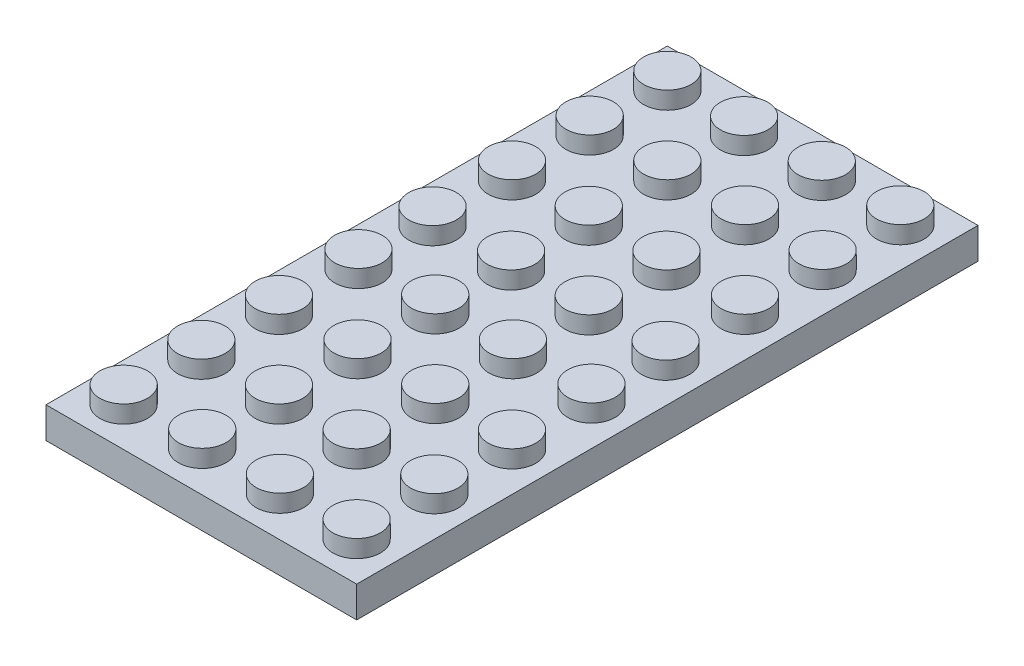
SolidWorks part; units mm, degrees
ref_plane "Front Plane" through (0, 0, 0) normal (0, 0, 1) x (1, 0, 0)
ref_plane "Top Plane" through (0, 0, 0) normal (0, 1, 0) x (1, 0, 0)
ref_plane "Right Plane" through (0, 0, 0) normal (1, 0, 0) x (0, 0, -1)
sketch "Sketch3" plane through (0, 0, 0) normal (0, 1, 0) x (1, 0, 0)
  line L0 (-16, 32) -> (-16, -32)
  line L4 (-16, 32) -> (16, 32)
  line L5 (16, 32) -> (16, -32)
  line L6 (16, -32) -> (-16, -32)
  dimension "D1" = 64
  dimension "D2" = 32
extrude "Boss-Extrude2" add sketch "Sketch3" along normal blind 3.2 contours L0 L6 L5 L4
sketch "Sketch4" plane through (0, 3.2, 0) normal (0, 1, 0) x (1, 0, 0)
  line L0 (-16, 32) -> (16, 32) construction
  circle A0 centre (-12, 28) radius 2.45
  circle A1 centre (-4, 27.9085) radius 2.45
  circle A2 centre (4, 27.9085) radius 2.45
  circle A3 centre (12, 28) radius 2.45
  circle A4 centre (12, 20) radius 2.45
  circle A5 centre (4, 20) radius 2.45
  circle A6 centre (-4, 20) radius 2.45
  circle A7 centre (-12, 20) radius 2.45
  circle A8 centre (12, 12) radius 2.45
  circle A9 centre (12, 3.817) radius 2.45
  circle A10 centre (4, 3.9085) radius 2.45
  circle A11 centre (4, 11.9085) radius 2.45
  circle A12 centre (-4, 11.9085) radius 2.45
  circle A13 centre (-4, 3.9085) radius 2.45
  circle A14 centre (-12, 3.817) radius 2.45
  circle A15 centre (-12, 12) radius 2.45
  circle A16 centre (4, -27.9085) radius 2.45
  circle A17 centre (12, -28) radius 2.45
  circle A18 centre (12, -20) radius 2.45
  circle A19 centre (4, -20) radius 2.45
  circle A20 centre (4, -11.9085) radius 2.45
  circle A21 centre (12, -12) radius 2.45
  circle A22 centre (12, -3.817) radius 2.45
  circle A23 centre (4, -3.9085) radius 2.45
  circle A24 centre (-4, -3.9085) radius 2.45
  circle A25 centre (-4, -11.9085) radius 2.45
  circle A26 centre (-4, -20) radius 2.45
  circle A27 centre (-4, -27.9085) radius 2.45
  circle A28 centre (-12, -28) radius 2.45
  circle A29 centre (-12, -20) radius 2.45
  circle A30 centre (-12, -12) radius 2.45
  circle A31 centre (-12, -3.817) radius 2.45
  dimension "D1" = 4.9
  dimension "D3" = 4
  dimension "D2" = 8
extrude "Boss-Extrude3" add sketch "Sketch4" along normal blind 1.8
sketch "Sketch5" plane through (0, 0, 0) normal (0, -1, 0) x (1, 0, 0)
  line L0 (-16, -32) -> (-16, 32) construction
  line L1 (-16, -32) -> (16, -32) construction
  line L9 (-14.5, 30.5) -> (14.5, 30.5)
  line L10 (-14.5, 30.5) -> (-14.5, -30.5)
  line L11 (-14.5, -30.5) -> (14.5, -30.5)
  line L12 (14.5, 30.5) -> (14.5, -30.5)
  dimension "D1" = 1.5
  dimension "D2" = 1.5
  dimension "D3" = 61
  dimension "D4" = 29
extrude "Cut-Extrude1" cut sketch "Sketch5" against normal blind 2
sketch "Sketch6" plane through (0, 2, 0) normal (0, -1, 0) x (1, 0, 0)
  line L0 (16, 32) -> (-16, 32) construction
  circle A0 centre (-8, 24) radius 3.2
  circle A1 centre (0, 24) radius 3.2
  circle A2 centre (8, 24) radius 3.2
  circle A3 centre (8, 16) radius 3.2
  circle A4 centre (0, 16) radius 3.2
  circle A5 centre (-8, 16) radius 3.2
  circle A6 centre (0, 8) radius 3.2
  circle A7 centre (8, 8) radius 3.2
  circle A8 centre (8, 0) radius 3.2
  circle A9 centre (0, 0) radius 3.2
  circle A10 centre (-8, 0) radius 3.2
  circle A11 centre (-8, 8) radius 3.2
  circle A12 centre (8, -24) radius 3.2
  circle A13 centre (8, -16) radius 3.2
  circle A14 centre (8, -8) radius 3.2
  circle A15 centre (0, -8) radius 3.2
  circle A16 centre (0, -16) radius 3.2
  circle A17 centre (0, -24) radius 3.2
  circle A18 centre (-8, -24) radius 3.2
  circle A19 centre (-8, -16) radius 3.2
  circle A20 centre (-8, -8) radius 3.2
  dimension "D1" = 6.4
  dimension "D2" = 8
  dimension "D3" = 8
extrude "Boss-Extrude4" add sketch "Sketch6" along normal blind 2
sketch "Sketch7" plane through (0, 2, 0) normal (0, -1, 0) x (1, 0, 0)
  line L1 (16, 32) -> (-16, 32) construction
  circle A0 centre (-8, -24) radius 2.5
  circle A1 centre (0, -24) radius 2.5
  circle A2 centre (8, -24) radius 2.5135
  circle A3 centre (-8, -16) radius 2.5
  circle A4 centre (0, -16) radius 2.5
  circle A5 centre (8, -16) radius 2.5
  circle A6 centre (-8, -8) radius 2.5
  circle A7 centre (0, -8) radius 2.5
  circle A8 centre (8, -8) radius 2.5
  circle A9 centre (-8, 8) radius 2.5
  circle A10 centre (0, 8) radius 2.5
  circle A11 centre (8, 8) radius 2.5135
  circle A12 centre (8, 0) radius 2.5
  circle A13 centre (0, 0) radius 2.5
  circle A14 centre (-8, 0) radius 2.5
  circle A15 centre (0, 16) radius 2.5
  circle A16 centre (8, 16) radius 2.5
  circle A17 centre (8, 24) radius 2.5
  circle A18 centre (0, 24) radius 2.5
  circle A19 centre (-8, 24) radius 2.5
  circle A20 centre (-8, 16) radius 2.5
  dimension "D1" = 5
  dimension "D2" = 8
  dimension "D3" = 8
extrude "Cut-Extrude2" cut sketch "Sketch7" along normal blind 2
